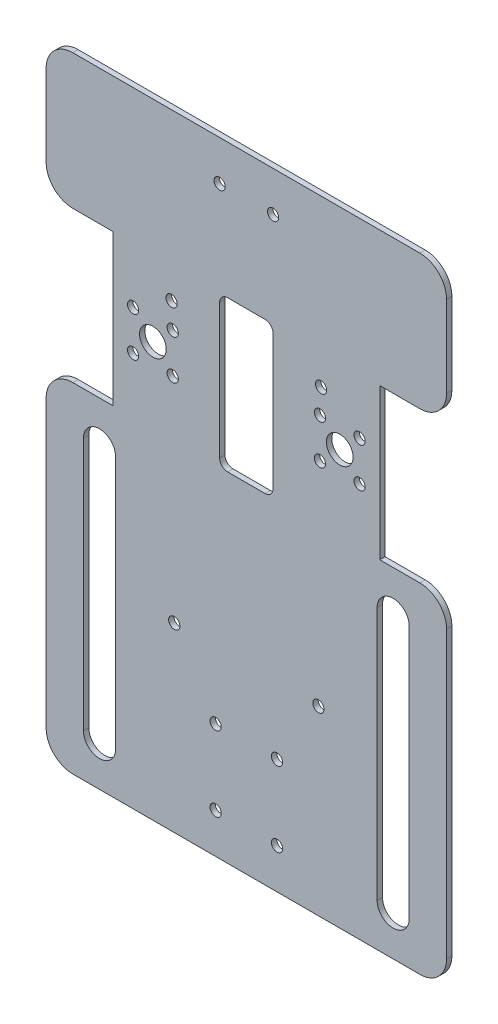
SolidWorks part; units mm, degrees
ref_plane "前视基准面" through (0, 0, 0) normal (0, 0, 1) x (1, 0, 0)
ref_plane "上视基准面" through (0, 0, 0) normal (0, 1, 0) x (1, 0, 0)
ref_plane "右视基准面" through (0, 0, 0) normal (1, 0, 0) x (0, 0, -1)
sketch "草图1" plane through (0, 0, 0) normal (0, 0, 1) x (1, 0, 0)
  line L0 (0, 0) -> (0, 160.8474) construction
  line L1 (0, 0) -> (160.8474, 0) construction
  line L2 (0, 0) -> (0, -160.8474) construction
  line L3 (0, 0) -> (-160.8474, 0) construction
  line L4 (75, 117) -> (-75, 117)
  line L5 (-75, 117) -> (-75, 66.5)
  line L6 (-75, 66.5) -> (-50, 66.5)
  line L7 (-50, 66.5) -> (-50, 10)
  line L8 (-50, 10) -> (-75, 10)
  line L9 (-75, 10) -> (-75, -117)
  line L10 (-75, -117) -> (75, -117)
  line L11 (75, 10) -> (75, -117)
  line L12 (50, 10) -> (75, 10)
  line L13 (50, 66.5) -> (50, 10)
  line L14 (75, 66.5) -> (50, 66.5)
  line L15 (75, 117) -> (75, 66.5)
  line L16 (-55, -6) -> (-55, -101) construction
  line L17 (-49, -6) -> (-49, -101)
  line L18 (-61, -6) -> (-61, -101)
  line L19 (0, -53.5) -> (-55, -53.5) construction
  line L20 (55, -6) -> (55, -101) construction
  line L21 (49, -6) -> (49, -101)
  line L22 (61, -6) -> (61, -101)
  arc A0 (-49, -6) -> (-61, -6) centre (-55, -6) ccw
  arc A1 (-61, -101) -> (-49, -101) centre (-55, -101) ccw
  arc A2 (49, -6) -> (61, -6) centre (55, -6) cw
  arc A3 (61, -101) -> (49, -101) centre (55, -101) cw
  point P9 (0, 0)
  point P15 (-55, -53.5)
  point P17 (0, -117)
  point P22 (0, 117)
  point P28 (-55, 0)
  point P33 (55, -53.5)
  dimension "D1" = 4
  dimension "D2" = 150
  dimension "D3" = 50.5
  dimension "D4" = 127
  dimension "D5" = 234
  dimension "D6" = 25
  dimension "D7" = 25
  dimension "D8" = 107
  dimension "D9" = 20
  dimension "D10" = 12
extrude "凸台-拉伸1" add sketch "草图1" along normal blind 2
fillet "圆角1" radius 10 8 edges at (75, 66.5, 1) (-75, -117, 1) (75, -117, 1) (75, 10, 1) (-75, 10, 1) (-75, 66.5, 1) (-75, 117, 1) (75, 117, 1)
sketch "草图2" plane through (0, 0, 0) normal (0, 0, -1) x (-1, 0, 0)
  line L0 (0, 117) -> (0, 0) construction
  line L1 (-65, 117) -> (65, 117) construction
  line L2 (0, 0) -> (-75, 0) construction
  line L3 (-75, -107) -> (-75, 0) construction
sketch "草图3" plane through (0, 0, 2) normal (0, 0, 1) x (1, 0, 0)
  line L0 (-75, 91.75) -> (0, 91.75) construction
  line L1 (-75, 107) -> (-75, 76.5) construction
  line L2 (0, 117) -> (0, 0) construction
  line L3 (0, 91.75) -> (0, 117) construction
  line L4 (-75, 102) -> (0, 102) construction
  line L5 (65, 117) -> (-65, 117) construction
  line L6 (-65, 66.5) -> (-50, 66.5) construction
  line L7 (-7, 66.5) -> (7, 66.5)
  line L8 (-10, 63.5) -> (-10, 13)
  line L9 (-7, 10) -> (7, 10)
  line L10 (10, 63.5) -> (10, 13)
  line L11 (0, 10) -> (0, 66.5) construction
  line L12 (-10, 38.25) -> (10, 38.25) construction
  line L13 (-35, 48.75) -> (-35, 38.25) construction
  line L14 (-50, 10) -> (-65, 10) construction
  line L15 (-35, 38.25) -> (-45.5, 38.25) construction
  line L16 (-49, -49) -> (49, -49) construction
  line L17 (-49, -101) -> (-49, -6) construction
  line L18 (49, -6) -> (49, -101) construction
  line L19 (-65, -117) -> (65, -117) construction
  line L20 (-49, -102) -> (49, -102) construction
  line L21 (-49, -88) -> (49, -88) construction
  circle A0 centre (0, 91.75) radius 2.1 construction
  circle A1 centre (-10, 102) radius 2.1
  arc A2 (7, 10) -> (10, 13) centre (7, 13) ccw
  arc A3 (-10, 13) -> (-7, 10) centre (-7, 13) ccw
  arc A4 (7, 66.5) -> (10, 63.5) centre (7, 63.5) cw
  arc A5 (-7, 66.5) -> (-10, 63.5) centre (-7, 63.5) ccw
  circle A6 centre (-35, 38.25) radius 5
  circle A7 centre (-35, 38.25) radius 10.5 construction
  circle A9 centre (-42.425, 30.8258) radius 2.1
  circle A10 centre (-42.4242, 45.675) radius 2.1
  circle A11 centre (-27.575, 45.6742) radius 2.1
  circle A12 centre (-27.5758, 30.825) radius 2.1
  circle A13 centre (27.5758, 30.825) radius 2.1
  circle A14 centre (27.575, 45.6742) radius 2.1
  circle A15 centre (42.4242, 45.675) radius 2.1
  circle A16 centre (42.425, 30.8258) radius 2.1
  circle A17 centre (35, 38.25) radius 5
  circle A18 centre (10, 102) radius 2.1
  circle A19 centre (27, -49) radius 2.1
  circle A20 centre (-27, -49) radius 2.1
  circle A21 centre (-11.5, -102) radius 2.1
  circle A22 centre (11.5, -102) radius 2.1
  circle A23 centre (11.5, -74) radius 2.1
  circle A24 centre (-11.5, -74) radius 2.1
  circle A25 centre (-28, 55) radius 2.1
  circle A26 centre (28, 55) radius 2.1
  point P15 (0, 38.25)
  point P32 (10, 66.5)
  point P35 (-10, 66.5)
  point P52 (-35, 38.25)
  dimension "D1" = 4.2
  dimension "D3" = 4.2
  dimension "D4" = 20
  dimension "D6" = 3
  dimension "D7" = 10
  dimension "D9" = 5.5
  dimension "D10" = 4.2
  dimension "D13" = 68
  dimension "D14" = 4.2
  dimension "D18" = 4.2
  dimension "D20" = 16.75
  dimension "D21" = 4.2
  dimension "D2" = 15
  dimension "D5" = 20
  dimension "D8" = 70
  dimension "D11" = 14.85
  dimension "D12" = 4
  dimension "D15" = 54
  dimension "D16" = 15
  dimension "D17" = 29
  dimension "D19" = 23
  dimension "D22" = 56
extrude "切除-拉伸1" cut sketch "草图3" against normal through all
